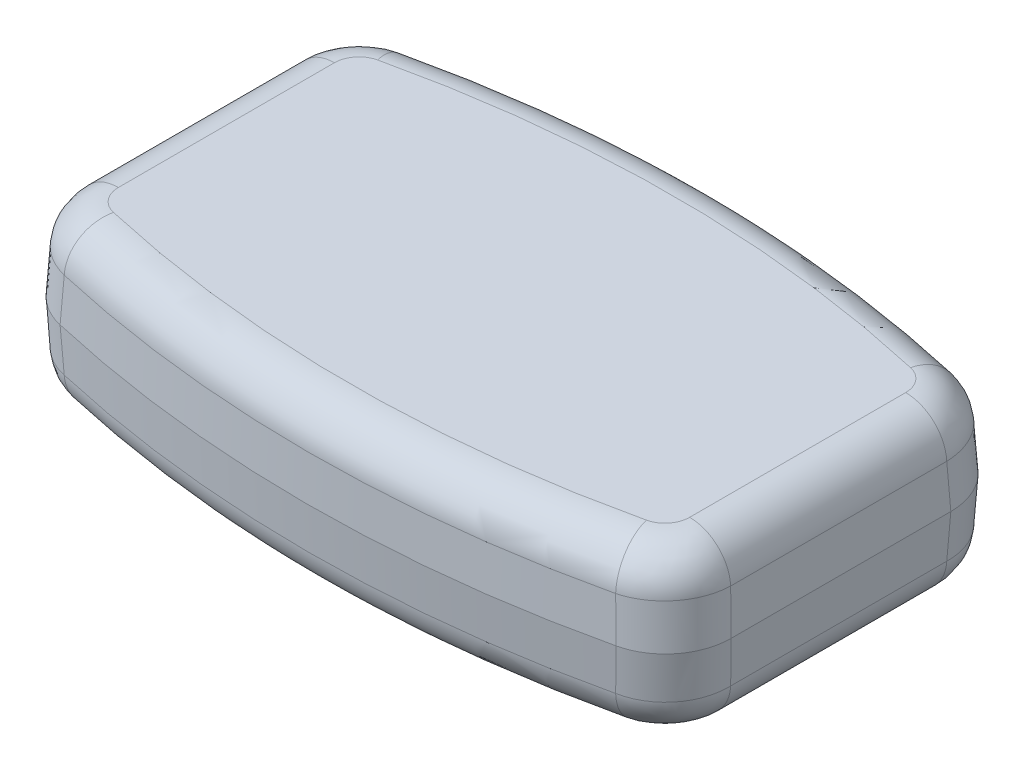
SolidWorks part; units mm, degrees
ref_plane "Front Plane" through (0, 0, 0) normal (0, 0, 1) x (1, 0, 0)
ref_plane "Top Plane" through (0, 0, 0) normal (0, 1, 0) x (1, 0, 0)
ref_plane "Right Plane" through (0, 0, 0) normal (1, 0, 0) x (0, 0, -1)
sketch "Sketch2" plane through (0, 0, 0) normal (0, 1, 0) x (1, 0, 0)
  line L0 (-91.3467, 0) -> (99.3696, 0) construction
  line L1 (0, 73.6963) -> (0, -82.4069) construction
  line L3 (-40, 25) -> (40, 25)
  line L4 (-40, 25) -> (-40, -25)
  line L5 (-40, -25) -> (40, -25)
  line L6 (40, 25) -> (40, -25)
  line L7 (-40, 25) -> (40, -25) construction
  line L8 (-40, -25) -> (40, 25) construction
  arc A0 (-40, 19.5683) -> (40, 19.5683) centre (0, -125) cw
  arc A1 (-40, -19.5683) -> (40, -19.5683) centre (0, 125) ccw
  point P5 (0, 0)
  dimension "D3" = 150
  dimension "D1" = 80
  dimension "D2" = 50
extrude "Boss-Extrude1" add sketch "Sketch2" along normal mid plane 20 draft 3 contours A1 L6 A0 L4
fillet "Fillet1" radius 8 8 edges
fillet "Fillet2" radius 5 16 edges at (-37.725, -10, -17.9312) (-39.4759, -10, 0) (-37.7424, -10, 17.9095) (0, -10, 24.4759) (37.725, -10, 17.9312) (39.4759, -10, 0) (37.7424, -10, -17.9095) (-37.725, 10, 17.9312) (-39.4759, 10, 0) (-37.7424, 10, -17.9095) (0, 10, -24.4759) (37.725, 10, -17.9312) (39.4759, 10, 0) (37.7424, 10, 17.9095) (0, -10, -24.4759) (0, 10, 24.4759)
